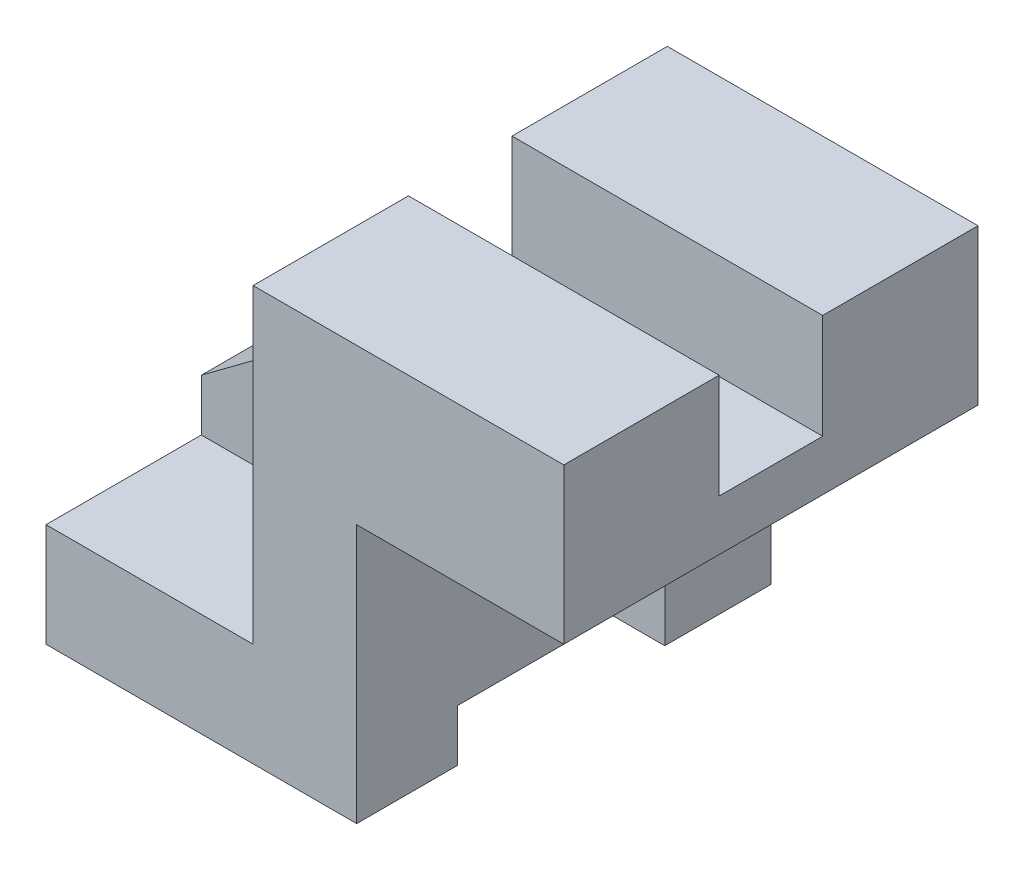
SolidWorks part; units mm, degrees
ref_plane "Front Plane" through (0, 0, 0) normal (0, 0, 1) x (1, 0, 0)
ref_plane "Top Plane" through (0, 0, 0) normal (0, 1, 0) x (1, 0, 0)
ref_plane "Right Plane" through (0, 0, 0) normal (1, 0, 0) x (0, 0, -1)
sketch "Sketch1" plane through (0, 0, 0) normal (0, 0, 1) x (1, 0, 0)
  line L0 (45.2683, 31.2766) -> (-14.7317, 31.2766)
  line L1 (-14.7317, 31.2766) -> (-14.7317, 11.0638)
  line L3 (-54.7317, -28.7234) -> (-54.7317, -48.7234)
  line L4 (-54.7317, -48.7234) -> (5.2683, -48.7234)
  line L5 (5.2683, -48.7234) -> (5.2683, 1.2766)
  line L6 (5.2683, 1.2766) -> (45.2683, 1.2766)
  line L7 (45.2683, 1.2766) -> (45.2683, 31.2766)
  line L8 (-54.7317, -28.7234) -> (-54.7317, -18.7234)
  line L9 (-54.7317, -18.7234) -> (-14.7317, 11.0638)
  line L11 (-54.7317, -28.7234) -> (-14.7317, -28.7234)
  line L12 (-14.7317, -28.7234) -> (-14.7317, 11.0638)
  dimension "D1" = 60
  dimension "D2" = 30
  dimension "D3" = 40
  dimension "D4" = 50
  dimension "D5" = 60
  dimension "D6" = 20
  dimension "D7" = 10
  dimension "D8" = 39.7872
extrude "Boss-Extrude1" add sketch "Sketch1" along normal mid plane 80 contours L12 L11 L3 L4 L5 L6 L7 L0 L1 | L11 L12 L9 L8
sketch "Sketch2" plane through (0, 0, 40) normal (0, 0, 1) x (1, 0, 0)
  line L0 (-54.7317, -18.7234) -> (-54.7317, -28.7234)
  line L1 (-14.7317, 11.0638) -> (-14.7317, -28.7234)
  line L2 (-54.7317, -28.7234) -> (-14.7317, -28.7234)
  line L4 (-54.7317, -18.7234) -> (-14.7317, 11.0638)
extrude "Cut-Extrude1" cut sketch "Sketch2" against normal blind 30
sketch "Sketch3" plane through (0, 0, -40) normal (0, 0, -1) x (-1, 0, 0)
  line L0 (14.7317, 11.0638) -> (54.7317, -18.7234)
  line L1 (54.7317, -28.7234) -> (14.7317, -28.7234)
  line L2 (54.7317, -18.7234) -> (54.7317, -28.7234)
  line L3 (14.7317, 11.0638) -> (14.7317, -28.7234)
extrude "Cut-Extrude2" cut sketch "Sketch3" against normal blind 30
sketch "Sketch4" plane through (-14.7317, 0, 0) normal (-1, 0, 0) x (0, 0, 1)
  line L0 (10, 11.0638) -> (10, 31.2766)
  line L2 (-10, 11.0638) -> (-10, 31.2766)
  line L3 (-10, 11.0638) -> (10, 11.0638)
  line L4 (-10, 31.2766) -> (10, 31.2766)
extrude "Cut-Extrude3" cut sketch "Sketch4" against normal up to next
sketch "Sketch5" plane through (-54.7317, 0, 0) normal (-1, 0, 0) x (0, 0, 1)
  line L0 (40, -48.7234) -> (-40, -48.7234) construction
  line L1 (-19.5024, -48.7234) -> (20.4976, -48.7234)
  line L2 (-19.5024, -48.7234) -> (-19.5024, -38.7234)
  line L3 (-19.5024, -38.7234) -> (20.4976, -38.7234)
  line L4 (20.4976, -48.7234) -> (20.4976, -38.7234)
  dimension "D1" = 40
  dimension "D2" = 10
extrude "Cut-Extrude4" cut sketch "Sketch5" against normal up to next
